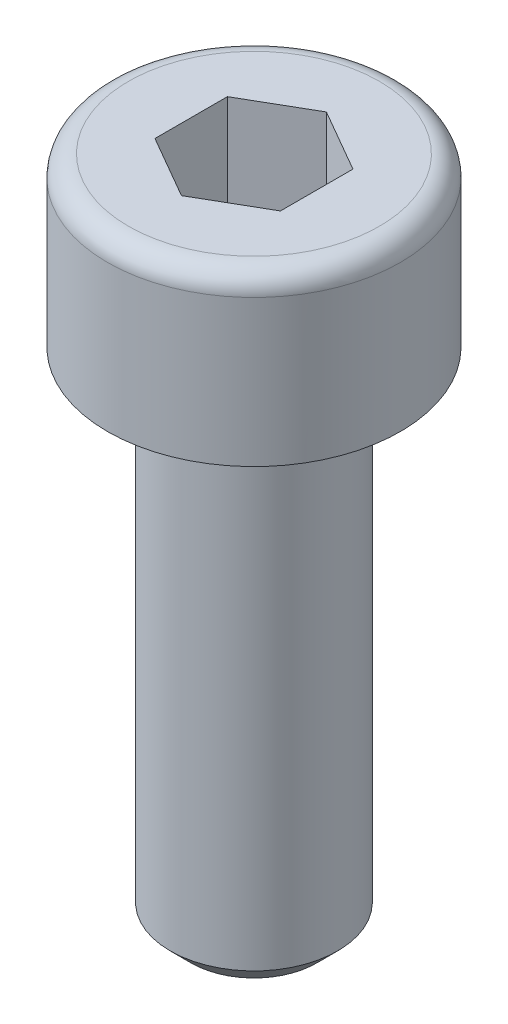
SolidWorks part; units mm, degrees
material "acero"
ref_plane "Alzado" through (0, 0, 0) normal (0, 0, 1) x (1, 0, 0)
ref_plane "Planta" through (0, 0, 0) normal (0, 1, 0) x (1, 0, 0)
ref_plane "Vista lateral" through (0, 0, 0) normal (1, 0, 0) x (0, 0, -1)
sketch "Croquis1" plane through (0, 0, 0) normal (0, 0, 1) x (1, 0, 0)
  line L0 (0, 0) -> (0, -60.9498) construction
  line L1 (0, 0) -> (3.5, 0)
  line L2 (3.5, 0) -> (3.5, -4)
  line L3 (3.5, -4) -> (2, -4)
  line L4 (2, -4) -> (2, -16)
  line L5 (2, -16) -> (0, -16)
  line L6 (0, -16) -> (0, 0)
  dimension "D1" = 12
  dimension "D2" = 4
  dimension "D3" = 7
  dimension "D4" = 4
revolve "Revolución1" add sketch "Croquis1" angle 360 about L0
sketch "Croquis2" plane through (0, 0, 0) normal (0, 1, 0) x (1, 0, 0)
  line L1 (1.5, 0.866) -> (0, 1.7321)
  line L2 (0, 1.7321) -> (-1.5, 0.866)
  line L3 (-1.5, 0.866) -> (-1.5, -0.866)
  line L4 (-1.5, -0.866) -> (0, -1.7321)
  line L5 (0, -1.7321) -> (1.5, -0.866)
  line L6 (1.5, -0.866) -> (1.5, 0.866)
  circle A0 centre (0, 0) radius 1.5 construction
  dimension "D1" = 3
extrude "Cortar-Extruir1" cut sketch "Croquis2" against normal blind 3
chamfer "Chaflán1" distance 0.5 angle 45 1 edges at (0, -16, 2)
fillet "Redondeo1" radius 0.5 1 edges at (0, 0, 3.5)
